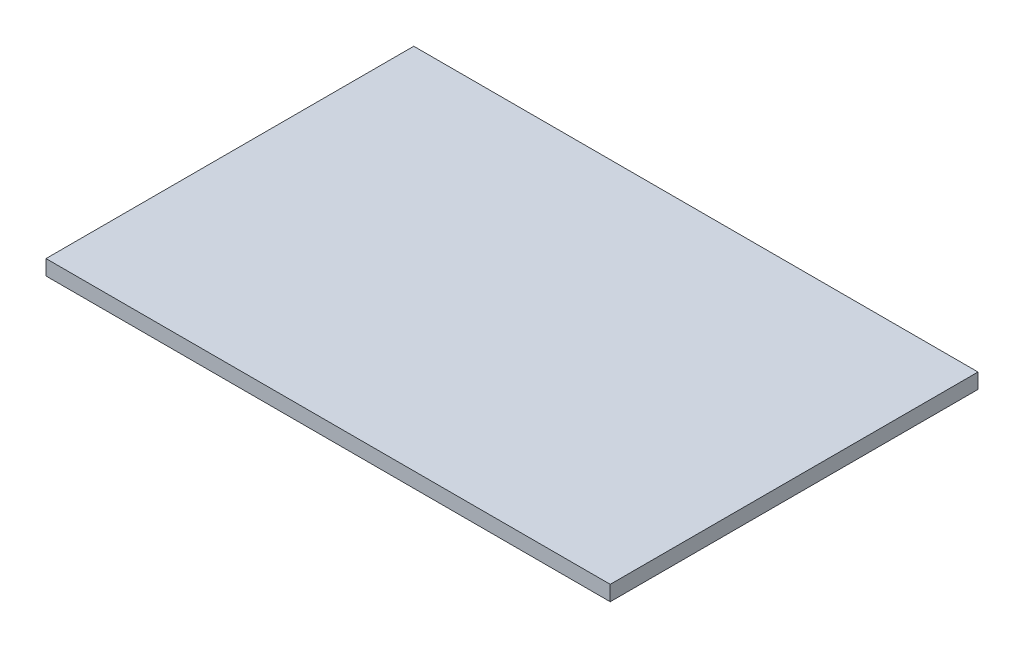
SolidWorks part; units mm, degrees
ref_plane "Front Plane" through (0, 0, 0) normal (0, 0, 1) x (1, 0, 0)
ref_plane "Top Plane" through (0, 0, 0) normal (0, 1, 0) x (1, 0, 0)
ref_plane "Right Plane" through (0, 0, 0) normal (1, 0, 0) x (0, 0, -1)
sketch "Sketch1" plane through (0, 0, 0) normal (0, 1, 0) x (1, 0, 0)
  line L1 (-56, 36.5) -> (56, 36.5)
  line L2 (-56, 36.5) -> (-56, -36.5)
  line L3 (-56, -36.5) -> (56, -36.5)
  line L4 (56, 36.5) -> (56, -36.5)
  line L5 (-56, 36.5) -> (56, -36.5) construction
  line L6 (-56, -36.5) -> (56, 36.5) construction
  point P0 (0, 0)
  dimension "D1" = 112
  dimension "D2" = 73
extrude "Boss-Extrude1" add sketch "Sketch1" along normal blind 3
